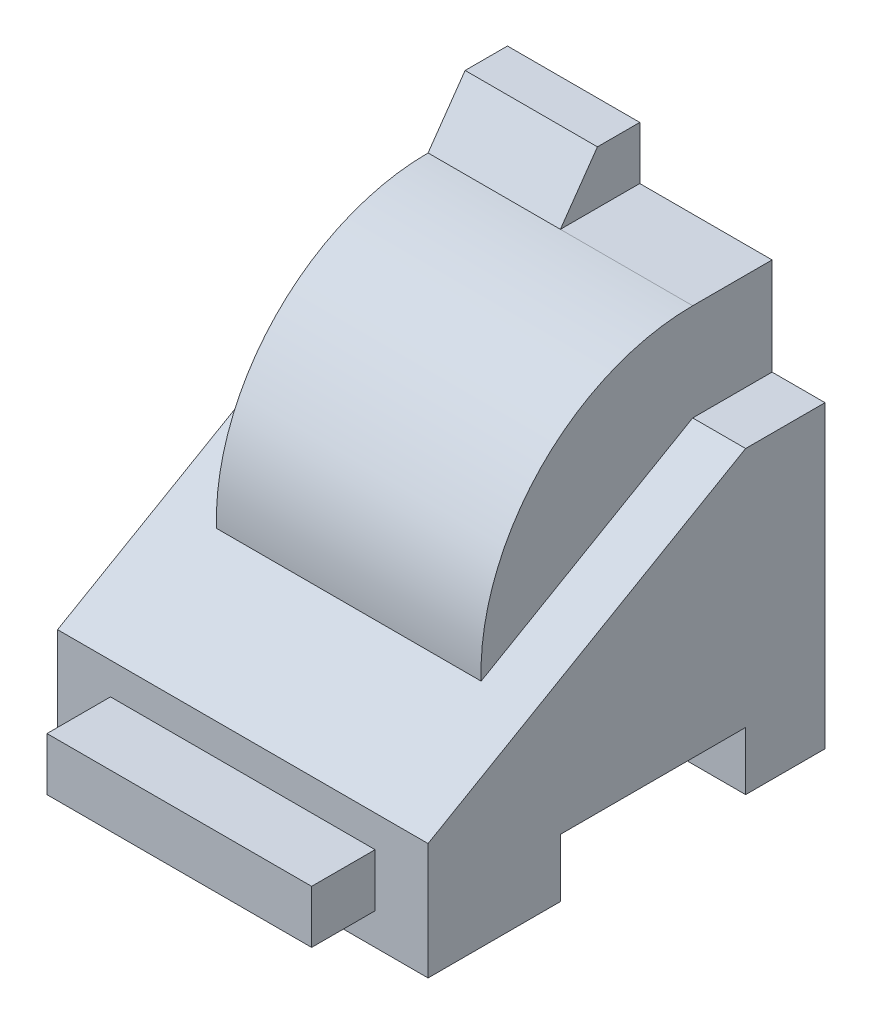
SolidWorks part; units mm, degrees
ref_plane "Front Plane" through (0, 0, 0) normal (0, 0, 1) x (1, 0, 0)
ref_plane "Top Plane" through (0, 0, 0) normal (0, 1, 0) x (1, 0, 0)
ref_plane "Right Plane" through (0, 0, 0) normal (1, 0, 0) x (0, 0, -1)
sketch "Sketch1" plane through (0, 0, 0) normal (1, 0, 0) x (0, 0, -1)
  line L0 (0, 0) -> (0, 56.641)
  line L1 (0, 56.641) -> (-15, 56.641)
  line L2 (-15, 56.641) -> (-75, 22)
  line L3 (-75, 22) -> (-75, 0)
  line L4 (-75, 0) -> (-50, 0)
  line L5 (-50, 0) -> (-50, 11)
  line L6 (-50, 11) -> (-15, 11)
  line L7 (-15, 11) -> (-15, 0)
  line L8 (-15, 0) -> (0, 0)
  dimension "D1" = 25
  dimension "D2" = 15
  dimension "D3" = 35
  dimension "D4" = 22
  dimension "D5" = 15
  dimension "D6" = 30
  dimension "D7" = 11
extrude "Boss-Extrude1" add sketch "Sketch1" along normal blind 70
sketch "Sketch2" plane through (0, 0, 75) normal (0, 0, 1) x (1, 0, 0)
  line L0 (70, 0) -> (0, 0) construction
  line L1 (10, 16) -> (60, 16)
  line L2 (10, 16) -> (10, 6)
  line L3 (10, 6) -> (60, 6)
  line L4 (60, 16) -> (60, 6)
  line L5 (70, 22) -> (70, 0) construction
  dimension "D1" = 10
  dimension "D2" = 6
  dimension "D3" = 50
  dimension "D4" = 10
extrude "Boss-Extrude2" add sketch "Sketch2" along normal blind 12
ref_plane "Plane1" through (35, 0, 0) normal (1, 0, 0) x (0, 0, -1)
sketch "Sketch3" plane through (35, 0, 0) normal (1, 0, 0) x (0, 0, -1)
  line L0 (-15, 56.641) -> (-15, 35) construction
  line L1 (-15, 56.641) -> (-15, 75) construction
  line L2 (-15, 75) -> (0, 75)
  line L3 (0, 56.641) -> (0, 75)
  line L4 (-15, 56.641) -> (-54.9741, 33.5619)
  line L5 (-15, 56.641) -> (-75, 22) construction
  line L7 (-15, 56.641) -> (0, 56.641)
  arc A0 (-15, 75) -> (-54.9741, 33.5619) centre (-15, 35) ccw
  dimension "D1" = 40
  dimension "D2" = 53
extrude "Boss-Extrude3" add sketch "Sketch3" along normal mid plane 50
sketch "Sketch4" plane through (35, 0, 0) normal (1, 0, 0) x (0, 0, -1)
  line L0 (0, 75) -> (0, 85)
  line L1 (0, 85) -> (-8, 85)
  line L2 (-8, 85) -> (-15, 75)
  line L3 (-15, 75) -> (0, 75)
  dimension "D1" = 10
  dimension "D2" = 8
extrude "Boss-Extrude4" add sketch "Sketch4" against normal up to surface (25 mm away) up to face at (10, 61.0668, 18.7551)
